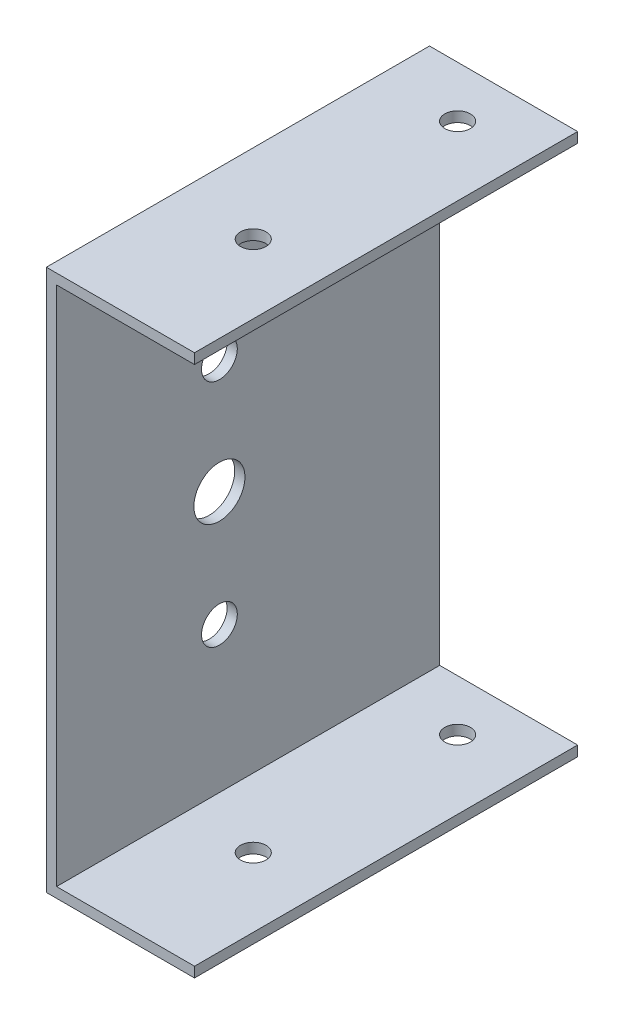
SolidWorks part; units mm, degrees
material "Liga 1060"
ref_plane "Plano frontal" through (0, 0, 0) normal (0, 0, 1) x (1, 0, 0)
ref_plane "Plano superior" through (0, 0, 0) normal (0, 1, 0) x (1, 0, 0)
ref_plane "Plano direito" through (0, 0, 0) normal (1, 0, 0) x (0, 0, -1)
sketch "Esboço1" plane through (0, 0, 0) normal (0, 1, 0) x (1, 0, 0)
  line L1 (13.5, -37.5) -> (-13.5, -37.5)
  line L2 (13.5, -37.5) -> (13.5, 37.5)
  line L3 (13.5, 37.5) -> (-13.5, 37.5)
  line L4 (-13.5, -37.5) -> (-13.5, 37.5)
  line L5 (13.5, -37.5) -> (-13.5, 37.5) construction
  line L6 (13.5, 37.5) -> (-13.5, -37.5) construction
  point P0 (0, 0)
  dimension "D1" = 27
  dimension "D2" = 75
extrude "Ressalto-extrusão1" add sketch "Esboço1" along normal blind 2
sketch "Esboço2" plane through (-13.5, 0, 0) normal (-1, 0, 0) x (0, 0, 1)
  line L0 (-37.5, 2) -> (-37.5, 0) construction
  line L1 (37.5, 0) -> (-37.5, 0)
  line L2 (37.5, 0) -> (37.5, 104)
  line L3 (37.5, 104) -> (-37.5, 104)
  line L4 (-37.5, 0) -> (-37.5, 104)
  dimension "D1" = 104
extrude "Ressalto-extrusão2" add sketch "Esboço2" along normal blind 2
sketch "Esboço3" plane through (0, 104, 0) normal (0, 1, 0) x (1, 0, 0)
  line L4 (-15.5, -37.5) -> (13.5, -37.5)
  line L5 (-15.5, 37.5) -> (-15.5, -37.5)
  line L6 (13.5, 37.5) -> (-15.5, 37.5)
  line L7 (13.5, -37.5) -> (13.5, 37.5)
  line L8 (-15.5, -37.5) -> (13.5, -37.5)
  line L9 (-15.5, 37.5) -> (-15.5, -37.5)
  line L10 (13.5, 37.5) -> (-15.5, 37.5)
  line L11 (13.5, -37.5) -> (13.5, 37.5)
  dimension "D1" = 0
extrude "Ressalto-extrusão3" add sketch "Esboço3" along normal blind 2
sketch "Esboço4" plane through (-15.5, 0, 0) normal (-1, 0, 0) x (0, 0, 1)
  arc A0 (4.5724, 60.4258) -> (9.4737, 59.4372) centre (5.625, 53) ccw construction
  arc A1 (4.5724, 60.4258) -> (9.4737, 59.4372) centre (5.625, 53) ccw
  circle A2 centre (5.625, 53) radius 7.5
  circle A3 centre (5.625, 53) radius 5
  dimension "D1" = 10
extrude "Corte-extrusão1" cut sketch "Esboço4" against normal blind 2 contours A3
sketch "Esboço5" plane through (0, 106, 0) normal (0, 1, 0) x (1, 0, 0)
  line L0 (13.5, 37.5) -> (-15.5, 37.5) construction
  line L1 (-15.5, -37.5) -> (13.5, -37.5) construction
  circle A0 centre (0, 27.5) radius 2.5
  circle A1 centre (0, -12.5) radius 2.5
  point P8 (0, 0)
  point P10 (0, 0)
  dimension "D1" = 5
  dimension "D2" = 5
  dimension "D3" = 10
  dimension "D4" = 25
extrude "Corte-extrusão2" cut sketch "Esboço5" against normal through all both and the other way through all
sketch "Esboço7" plane through (-15.5, 0, 0) normal (-1, 0, 0) x (0, 0, 1)
  circle A0 centre (5.625, 75.5) radius 3.5
  circle A1 centre (5.625, 30.5) radius 3.5
  circle A2 centre (5.625, 53) radius 5 construction
  dimension "D1" = 7
  dimension "D2" = 7
  dimension "D4" = 45
  dimension "D3" = 22.5
extrude "Corte-extrusão3" cut sketch "Esboço7" against normal blind 10
